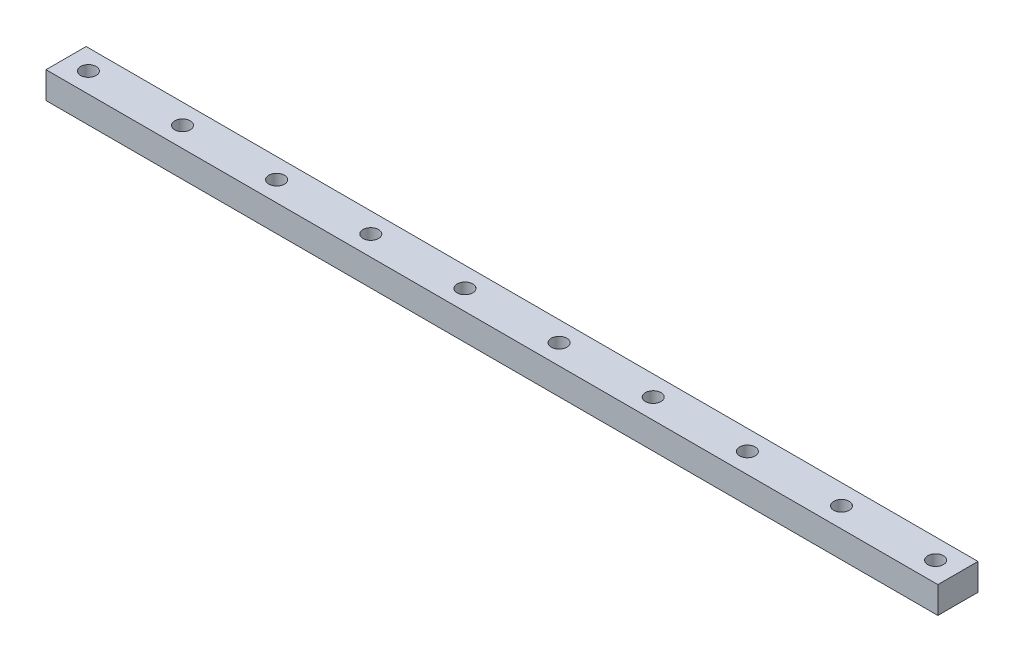
SolidWorks part; units mm, degrees
ref_plane "Front Plane" through (0, 0, 0) normal (0, 0, 1) x (1, 0, 0)
ref_plane "Top Plane" through (0, 0, 0) normal (0, 1, 0) x (1, 0, 0)
ref_plane "Right Plane" through (0, 0, 0) normal (1, 0, 0) x (0, 0, -1)
sketch "Sketch1" plane through (0, 0, 0) normal (0, 1, 0) x (1, 0, 0)
  line L1 (0, 0) -> (200, 0)
  line L2 (0, 0) -> (0, 9)
  line L3 (0, 9) -> (200, 9)
  line L4 (200, 0) -> (200, 9)
  dimension "D1" = 200
  dimension "D2" = 9
extrude "Boss-Extrude1" add sketch "Sketch1" along normal blind 6
sketch "Sketch2" plane through (0, 6, 0) normal (0, 1, 0) x (1, 0, 0)
  line L0 (0, 9) -> (0, 0) construction
  line L1 (0, 4.5) -> (35.1031, 4.5) construction
  circle A0 centre (5, 4.5) radius 1.75
  dimension "D1" = 3.5
  dimension "D2" = 5
extrude "Cut-Extrude1" cut sketch "Sketch2" against normal blind 6
pattern_linear "LPattern1" count 10 spacing 21.1111 along (1, 0, 0) of "Cut-Extrude1"
